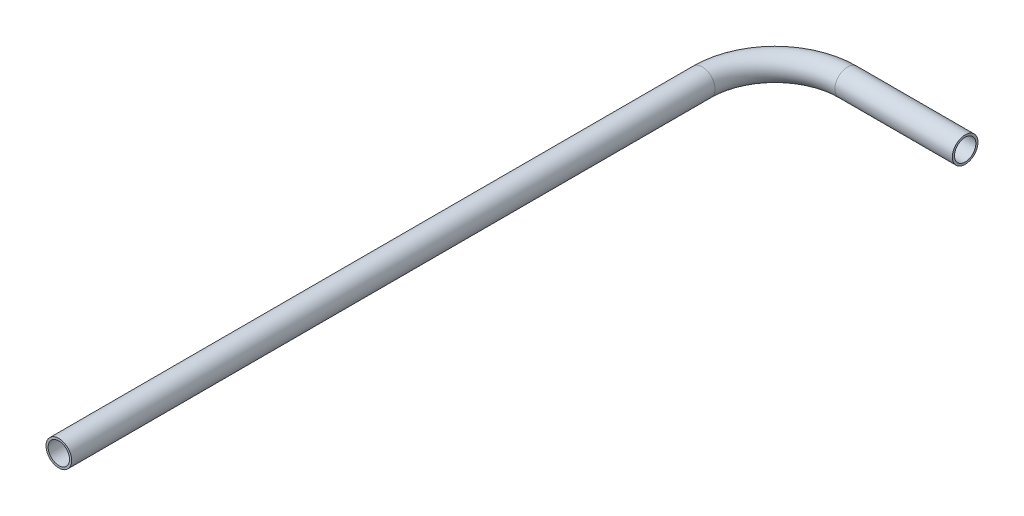
SolidWorks part; units mm, degrees
material "Aluminum Bronze"
ref_plane "Front Plane" through (0, 0, 0) normal (0, 0, 1) x (1, 0, 0)
ref_plane "Top Plane" through (0, 0, 0) normal (0, 1, 0) x (1, 0, 0)
ref_plane "Right Plane" through (0, 0, 0) normal (1, 0, 0) x (0, 0, -1)
sketch "Sketch1" plane through (0, 0, 0) normal (0, 1, 0) x (1, 0, 0)
  line L0 (0, 0) -> (0, 150.5)
  line L1 (17, 167.5) -> (44.5, 167.5)
  arc A0 (17, 167.5) -> (0, 150.5) centre (17, 150.5) ccw
  point P6 (0, 167.5)
  point P7 (0, 0)
  dimension "D3" = 17
  dimension "D1" = 167.5
  dimension "D2" = 44.5
sketch "Sketch2" plane through (0, 0, 0) normal (0, 0, 1) x (1, 0, 0)
  circle A0 centre (0, 0) radius 3
  circle A1 centre (0, 0) radius 2.5
sweep "Sweep1" add profiles "Sketch2" path "Sketch1"
